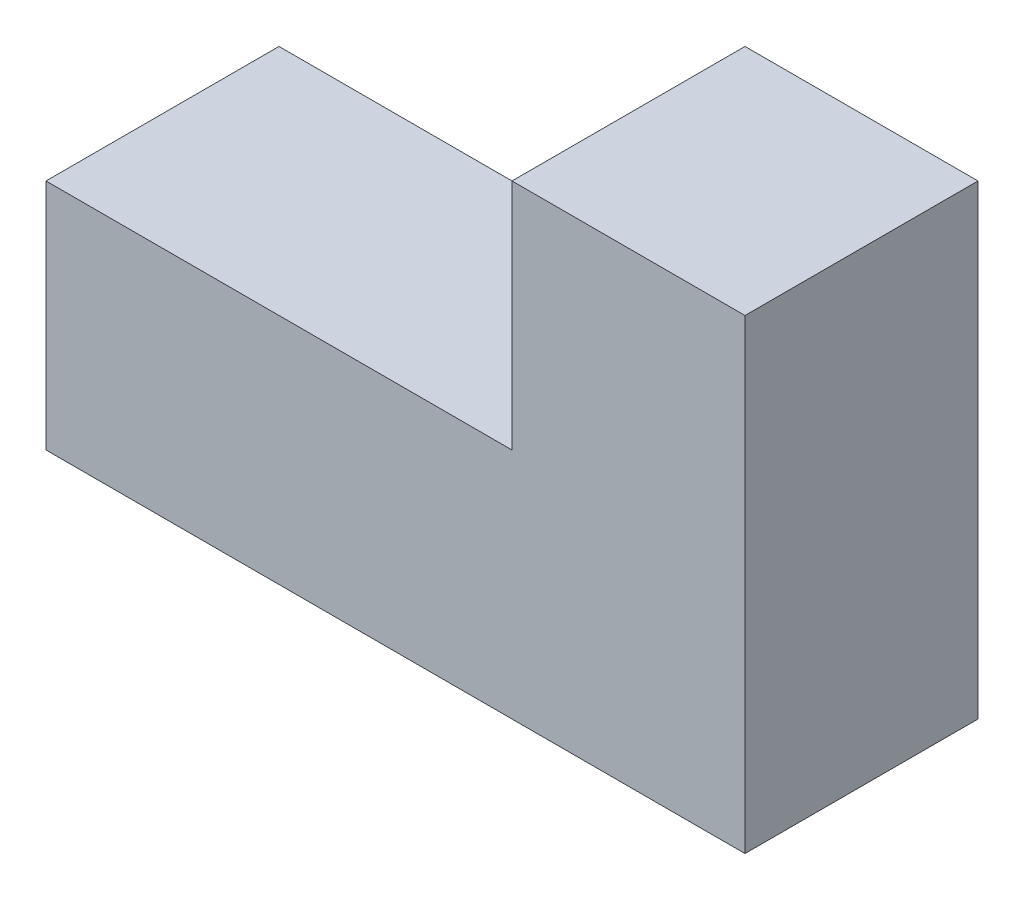
SolidWorks part; units mm, degrees
ref_plane "Plan de face" through (0, 0, 0) normal (0, 0, 1) x (1, 0, 0)
ref_plane "Plan de dessus" through (0, 0, 0) normal (0, 1, 0) x (1, 0, 0)
ref_plane "Plan de droite" through (0, 0, 0) normal (1, 0, 0) x (0, 0, -1)
sketch "Esquisse2" plane through (0, 0, 0) normal (0, 0, 1) x (1, 0, 0)
  line L0 (0, 0) -> (90, 0)
  line L1 (90, 0) -> (90, 60)
  line L2 (90, 60) -> (60, 60)
  line L3 (60, 60) -> (60, 30)
  line L4 (60, 30) -> (0, 30)
  line L5 (0, 30) -> (0, 0)
  dimension "D1" = 90
  dimension "D2" = 60
  dimension "D3" = 30
  dimension "D4" = 60
extrude "Boss.-Extru.1" add sketch "Esquisse2" along normal blind 30
